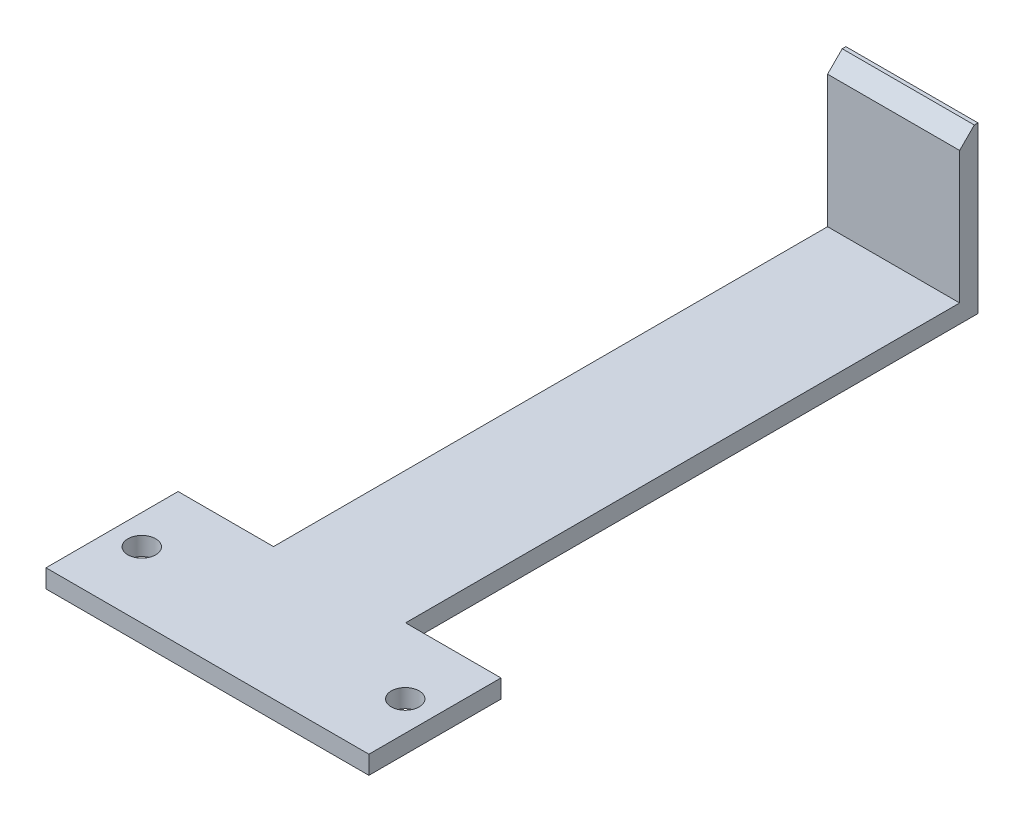
SolidWorks part; units mm, degrees
ref_plane "Front Plane" through (0, 0, 0) normal (0, 0, 1) x (1, 0, 0)
ref_plane "Top Plane" through (0, 0, 0) normal (0, 1, 0) x (1, 0, 0)
ref_plane "Right Plane" through (0, 0, 0) normal (1, 0, 0) x (0, 0, -1)
sketch "Sketch1" plane through (0, 0, 0) normal (0, 1, 0) x (1, 0, 0)
  line L1 (27.94, -11.43) -> (-27.94, -11.43)
  line L2 (27.94, -11.43) -> (27.94, 11.43)
  line L3 (27.94, 11.43) -> (-27.94, 11.43)
  line L4 (-27.94, -11.43) -> (-27.94, 11.43)
  line L5 (27.94, -11.43) -> (-27.94, 11.43) construction
  line L6 (27.94, 11.43) -> (-27.94, -11.43) construction
  line L7 (0, 11.43) -> (-11.43, 11.43)
  line L8 (0, 11.43) -> (0, 110.49)
  line L9 (0, 110.49) -> (-11.43, 110.49)
  line L10 (-11.43, 11.43) -> (-11.43, 110.49)
  line L11 (0, 11.43) -> (11.43, 11.43)
  line L12 (0, 11.43) -> (0, 110.49)
  line L13 (0, 110.49) -> (11.43, 110.49)
  line L14 (11.43, 11.43) -> (11.43, 110.49)
  circle A0 centre (-22.7965, 0) radius 2.413
  circle A1 centre (22.7965, 0) radius 2.413
  point P0 (0, 0)
  dimension "D5" = 4.826
  dimension "D6" = 4.826
  dimension "D7" = 45.593
  dimension "D8" = 22.7965
  dimension "D9" = 99.06
  dimension "D1" = 55.88
  dimension "D2" = 22.86
  dimension "D3" = 11.43
  dimension "D4" = 11.43
extrude "Boss-Extrude1" add sketch "Sketch1" along normal blind 3.175 contours L10 L3 L8 L9 | L3 L14 L13 L8 | L4 L1 L2 L3 A1 A0
sketch "Sketch2" plane through (0, 3.175, 0) normal (0, 1, 0) x (1, 0, 0)
  line L0 (11.43, 11.43) -> (11.43, 110.49) construction
  line L1 (-11.43, 110.49) -> (11.43, 110.49)
  line L2 (-11.43, 110.49) -> (-11.43, 107.315)
  line L3 (-11.43, 107.315) -> (11.43, 107.315)
  line L4 (11.43, 110.49) -> (11.43, 107.315)
  dimension "D1" = 3.175
extrude "Boss-Extrude2" add sketch "Sketch2" along normal blind 25.4
chamfer "Chamfer1" distance 2.54 angle 45 1 edges at (0, 28.575, -107.315)
